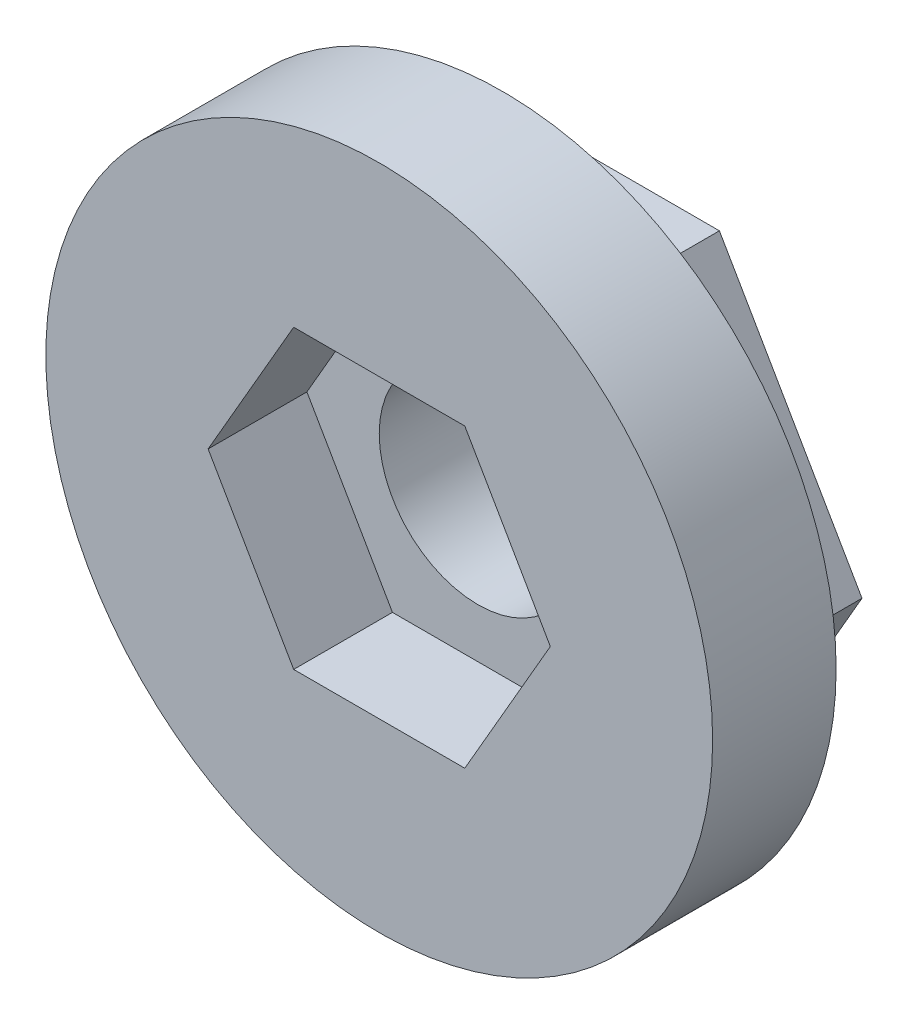
SolidWorks part; units mm, degrees
material "ABS"
ref_plane "Front Plane" through (0, 0, 0) normal (0, 0, 1) x (1, 0, 0)
ref_plane "Top Plane" through (0, 0, 0) normal (0, 1, 0) x (1, 0, 0)
ref_plane "Right Plane" through (0, 0, 0) normal (1, 0, 0) x (0, 0, -1)
sketch "Sketch1" plane through (0, 0, 0) normal (0, 0, 1) x (1, 0, 0)
  line L1 (11.547, 0) -> (5.7735, 10)
  line L2 (5.7735, 10) -> (-5.7735, 10)
  line L3 (-5.7735, 10) -> (-11.547, 0)
  line L4 (-11.547, 0) -> (-5.7735, -10)
  line L5 (-5.7735, -10) -> (5.7735, -10)
  line L6 (5.7735, -10) -> (11.547, 0)
  circle A0 centre (0, 0) radius 10 construction
  dimension "D1" = 20
extrude "Boss-Extrude1" add sketch "Sketch1" along normal blind 3
sketch "Sketch3" plane through (0, 0, 3) normal (0, 0, 1) x (1, 0, 0)
  circle A0 centre (0, 0) radius 13.5
  dimension "D1" = 27
extrude "Boss-Extrude2" add sketch "Sketch3" along normal blind 5
sketch "Sketch4" plane through (0, 0, 8) normal (0, 0, 1) x (1, 0, 0)
  line L1 (3.4641, -6) -> (6.9282, 0)
  line L2 (6.9282, 0) -> (3.4641, 6)
  line L3 (3.4641, 6) -> (-3.4641, 6)
  line L4 (-3.4641, 6) -> (-6.9282, 0)
  line L5 (-6.9282, 0) -> (-3.4641, -6)
  line L6 (-3.4641, -6) -> (3.4641, -6)
  circle A0 centre (0, 0) radius 6 construction
  dimension "D1" = 12
extrude "Cut-Extrude1" cut sketch "Sketch4" against normal blind 4
sketch "Sketch6" plane through (0, 0, 0) normal (0, 0, -1) x (-1, 0, 0)
  circle A0 centre (0, 0) radius 4
  dimension "D1" = 8
extrude "Cut-Extrude2" cut sketch "Sketch6" against normal through all
